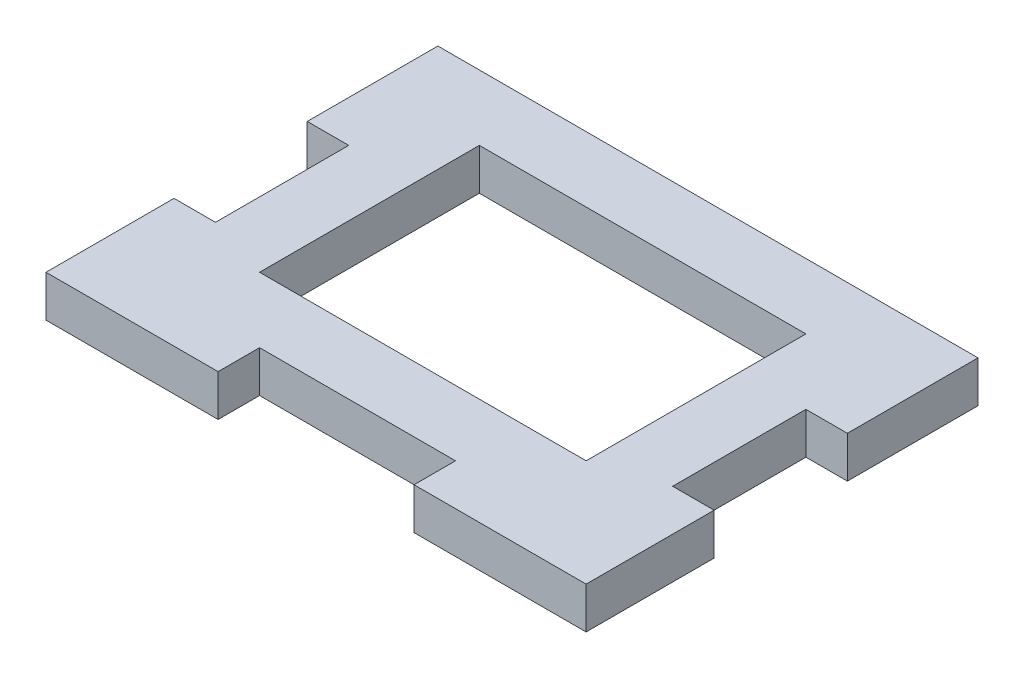
SolidWorks part; units mm, degrees
ref_plane "Front Plane" through (0, 0, 0) normal (0, 0, 1) x (1, 0, 0)
ref_plane "Top Plane" through (0, 0, 0) normal (0, 1, 0) x (1, 0, 0)
ref_plane "Right Plane" through (0, 0, 0) normal (1, 0, 0) x (0, 0, -1)
sketch "Sketch1" plane through (0, 0, 0) normal (0, 1, 0) x (1, 0, 0)
  line L1 (0, 0) -> (41.35, 0)
  line L2 (0, 0) -> (0, 30)
  line L3 (0, 30) -> (41.35, 30)
  line L4 (41.35, 0) -> (41.35, 30)
  dimension "D1" = 41.35
  dimension "D2" = 30
extrude "Boss-Extrude1" add sketch "Sketch1" along normal blind 3.175
sketch "Sketch2" plane through (0, 0, 0) normal (0, -1, 0) x (1, 0, 0)
  line L1 (0, -30) -> (0, 0) construction
  line L2 (3.175, -20) -> (0, -20)
  line L3 (3.175, -20) -> (3.175, -9.8)
  line L4 (3.175, -9.8) -> (0, -9.8)
  line L5 (28.275, -3.175) -> (13.075, -3.175) construction
  line L6 (0, -20) -> (0, -9.8)
  line L7 (3.175, -9.8) -> (0, -9.8) construction
  line L8 (41.35, 0) -> (41.35, -30) construction
  line L9 (38.175, -9.8) -> (41.35, -9.8)
  line L10 (38.175, -9.8) -> (38.175, -20)
  line L11 (38.175, -20) -> (41.35, -20)
  line L12 (41.35, -9.8) -> (41.35, -20)
  line L13 (41.35, -20) -> (38.175, -20) construction
  line L18 (13.175, -3.175) -> (28.175, -3.175)
  line L19 (13.175, -3.175) -> (13.175, 0)
  line L20 (13.175, 0) -> (28.175, 0)
  line L21 (28.175, -3.175) -> (28.175, 0)
  line L22 (0, 0) -> (41.35, 0) construction
  point P33 (20.675, -3.175)
  point P34 (20.675, 0)
  dimension "D1" = 15
extrude "Cut-Extrude1" cut sketch "Sketch2" against normal through all
sketch "Sketch3" plane through (0, 3.175, 0) normal (0, 1, 0) x (1, 0, 0)
  line L32 (33.175, 8.175) -> (33.175, 25)
  line L33 (33.175, 25) -> (8.175, 25)
  line L34 (8.175, 25) -> (8.175, 8.175)
  line L35 (8.175, 8.175) -> (33.175, 8.175)
  line L36 (33.175, 8.175) -> (33.175, 25)
  line L37 (33.175, 25) -> (8.175, 25)
  line L38 (8.175, 25) -> (8.175, 8.175)
  line L39 (8.175, 8.175) -> (33.175, 8.175)
  dimension "D1" = 5
extrude "Cut-Extrude2" cut sketch "Sketch3" against normal through all and the other way through all
